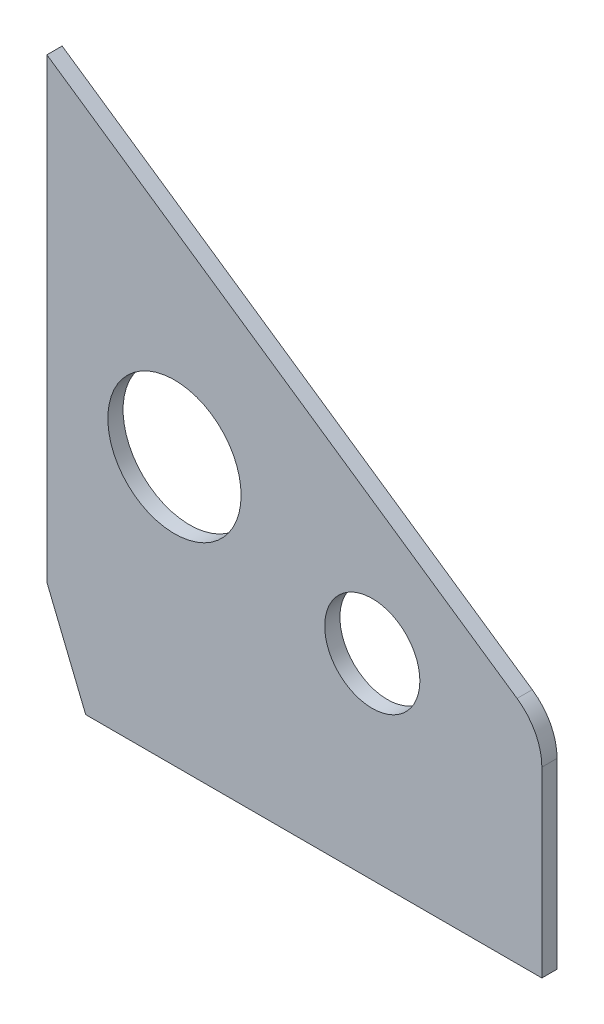
SolidWorks part; units mm, degrees
ref_plane "前视基准面" through (0, 0, 0) normal (0, 0, 1) x (1, 0, 0)
ref_plane "上视基准面" through (0, 0, 0) normal (0, 1, 0) x (1, 0, 0)
ref_plane "右视基准面" through (0, 0, 0) normal (1, 0, 0) x (0, 0, -1)
sketch "草图1" plane through (0, 0, 0) normal (0, 0, 1) x (1, 0, 0)
  line L0 (-26.7165, 615.2902) -> (-146.5344, 615.2902)
  line L1 (-156.7165, 760.2902) -> (-156.7165, 640.2902)
  line L2 (-26.7165, 663.2509) -> (-26.7165, 615.2902)
  line L3 (-156.7165, 640.2902) -> (-146.5344, 615.2902)
  line L4 (-156.7165, 760.2902) -> (-33.234, 675.6221)
  arc A0 (-26.7165, 663.2509) -> (-33.234, 675.6221) centre (-41.7165, 663.2509) ccw
  circle A1 centre (-123.2142, 685.5894) radius 17.5
  circle A2 centre (-71.2581, 666.8408) radius 12.5
extrude "凸台-拉伸1" add sketch "草图1" along normal blind 4
